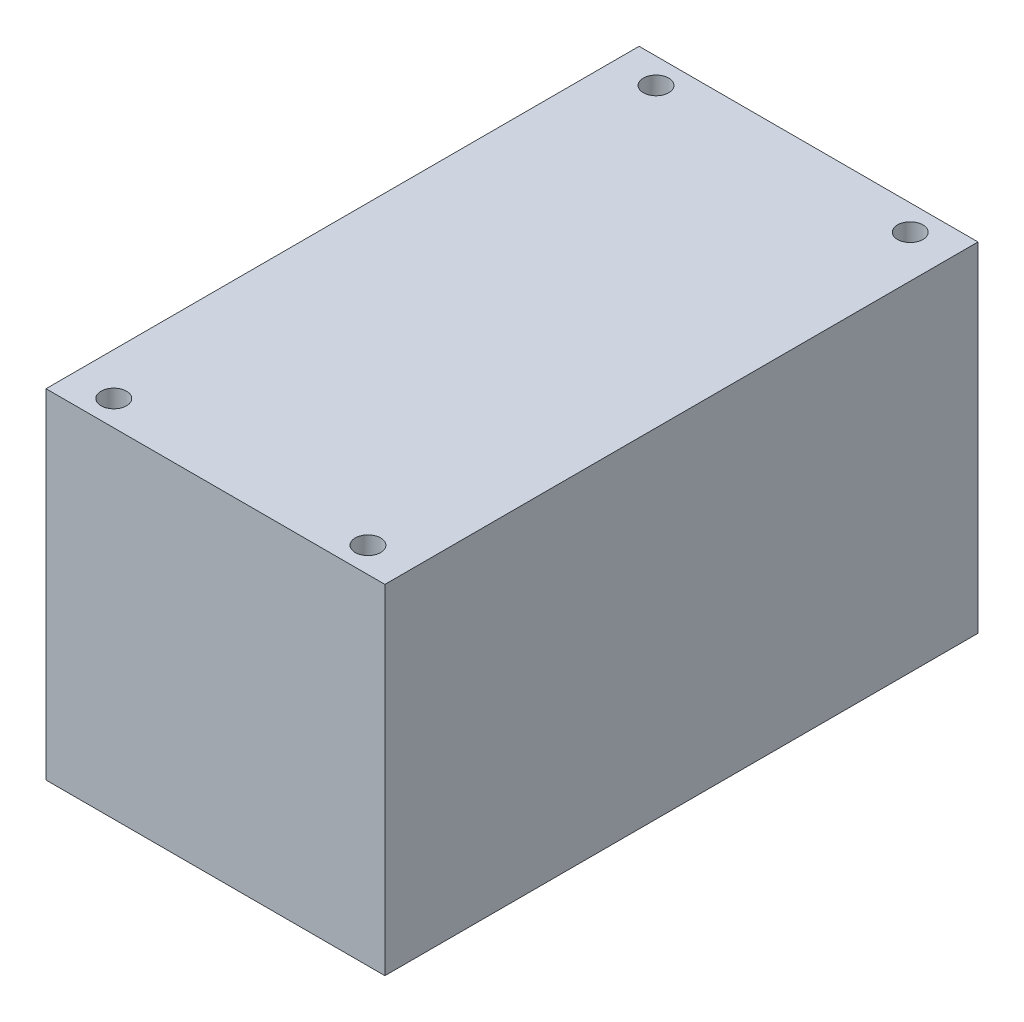
SolidWorks part; units mm, degrees
material "AISI 316 退火不锈钢条 (SS)"
ref_plane "前视基准面" through (0, 0, 0) normal (0, 0, 1) x (1, 0, 0)
ref_plane "上视基准面" through (0, 0, 0) normal (0, 1, 0) x (1, 0, 0)
ref_plane "右视基准面" through (0, 0, 0) normal (1, 0, 0) x (0, 0, -1)
sketch "草图1" plane through (0, 0, 0) normal (0, 0, 1) x (1, 0, 0)
  line L1 (-20, 20) -> (20, 20)
  line L2 (-20, 20) -> (-20, -20)
  line L3 (-20, -20) -> (20, -20)
  line L4 (20, 20) -> (20, -20)
  line L5 (-20, 20) -> (20, -20) construction
  line L6 (-20, -20) -> (20, 20) construction
  point P0 (0, 0)
  dimension "D1" = 40
  dimension "D2" = 40
extrude "凸台-拉伸1" add sketch "草图1" against normal blind 70
sketch "草图2" plane through (0, 0, 0) normal (0, 0, -1) x (-1, 0, 0)
  line L0 (20, -20) -> (4.5, -20) construction
  line L1 (20, -20) -> (-20, -20) construction
  line L2 (4.5, -20) -> (4.5, -1) construction
  line L3 (4.5, -1) -> (6.3732, -1) construction
  circle A0 centre (4.5, -1) radius 1.8732
  dimension "D1" = 19
  dimension "D2" = 15.5
ref_plane "405H" through (0, -1, 0) normal (0, 1, 0) x (-1, 0, 0)
ref_plane "405V" through (-4.5, 0, 0) normal (-1, 0, 0) x (0, 1, 0)
sketch "草图3" plane through (0, 20, 0) normal (0, 1, 0) x (1, 0, 0)
  line L0 (20, 70) -> (-20, 70) construction
  line L1 (-15, 67) -> (15, 67)
  line L2 (-15, 67) -> (-15, 3)
  line L3 (-15, 3) -> (15, 3)
  line L4 (15, 67) -> (15, 3)
  line L5 (0, 70) -> (0, 0) construction
  line L6 (0, 67) -> (0, 3) construction
  dimension "D1" = 64
  dimension "D2" = 30
  dimension "D3" = 3
hole_wizard "Ø3.0 (3) 直径孔1" positions "3D草图1" profile "草图4" hole size "Ø3.0" standard "GB" end condition through all
sketch3d "3D草图1"
  point P0 (-15, 20, -67)
  point P3 (15, 20, -67)
  point P6 (-15, 20, -3)
  point P9 (15, 20, -3)
sketch "草图4" plane through (-15, 20, -67) normal (1, 0, 0) x (0, 0, 1)
  line L0 (0, 0) -> (0, 40)
  line L1 (0, 40) -> (1.5, 40)
  line L2 (1.5, 40) -> (1.5, 0)
  line L5 (1.5, 0) -> (0, 0)
  line L11 (0, -6.35) -> (0, 107.95) construction
  dimension "通孔孔直径" = 3
  dimension "通孔孔深度" = 40
